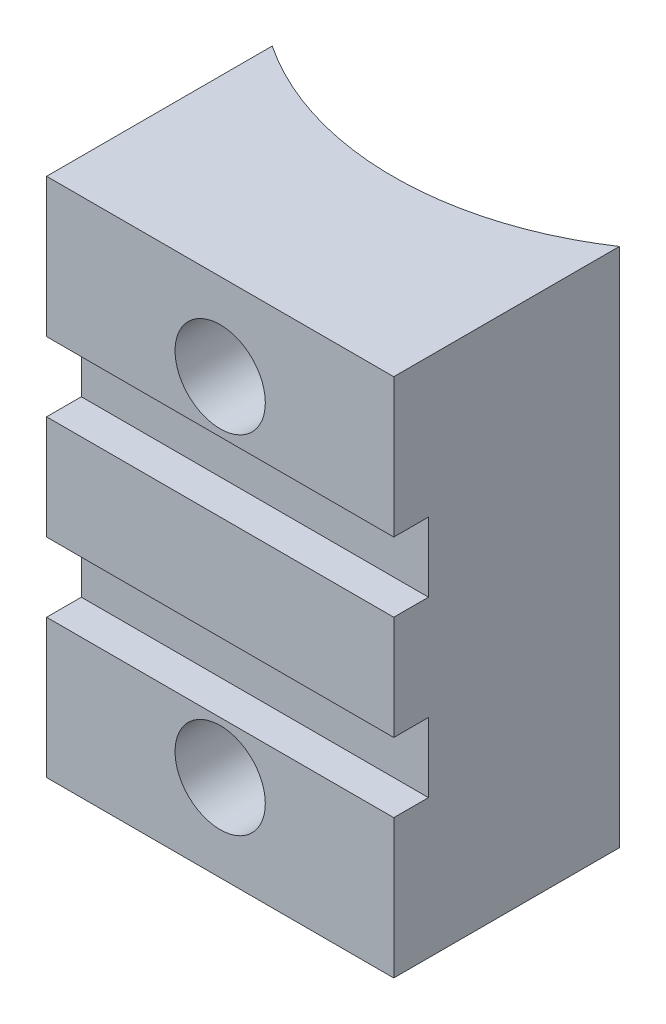
SolidWorks part; units mm, degrees
material "ABS"
ref_plane "Front Plane" through (0, 0, 0) normal (0, 0, 1) x (1, 0, 0)
ref_plane "Top Plane" through (0, 0, 0) normal (0, 1, 0) x (1, 0, 0)
ref_plane "Right Plane" through (0, 0, 0) normal (1, 0, 0) x (0, 0, -1)
sketch "Sketch1" plane through (0, 0, 0) normal (0, 1, 0) x (1, 0, 0)
  line L0 (0, 0) -> (20, 0)
  line L1 (20, 0) -> (20, 13)
  line L2 (0, 13) -> (0, 0)
  line L3 (10, 27.9666) -> (10, 0) construction
  arc A0 (20, 13) -> (0, 13) centre (10, 27.9666) cw
  dimension "D1" = 18
  dimension "D2" = 20
  dimension "D3" = 13
extrude "Boss-Extrude1" add sketch "Sketch1" along normal blind 30
sketch "Sketch2" plane through (0, 0, 0) normal (0, 0, 1) x (1, 0, 0)
  line L0 (10, 30) -> (10, 28.9885) construction
  line L1 (0, 30) -> (20, 30) construction
  line L2 (0, 0) -> (20, 0) construction
  circle A0 centre (10, 25) radius 2.6
  circle A2 centre (10, 5) radius 2.6
  dimension "D1" = 5.2
  dimension "D2" = 5
  dimension "D3" = 5
extrude "Cut-Extrude1" cut sketch "Sketch2" against normal up to next
sketch "Sketch3" plane through (0, 0, 0) normal (0, 0, 1) x (1, 0, 0)
  circle A0 centre (10, 25) radius 4.4
  circle A2 centre (10, 5) radius 4.4
  dimension "D1" = 8.8
extrude "Cut-Extrude2" cut sketch "Sketch3" against normal up to next from offset 4.5 offset against normal yes
sketch "Sketch4" plane through (20, 0, 0) normal (1, 0, 0) x (0, 0, -1)
  line L0 (0, 22) -> (2, 22)
  line L1 (0, 30) -> (0, 0) construction
  line L2 (2, 22) -> (2, 18)
  line L3 (2, 18) -> (0, 18)
  line L4 (0, 18) -> (0, 22)
  line L5 (0, 12) -> (2, 12)
  line L6 (2, 12) -> (2, 8)
  line L7 (2, 8) -> (0, 8)
  line L8 (0, 8) -> (0, 12)
  line L9 (0, 30) -> (13, 30) construction
  line L10 (0, 0) -> (13, 0) construction
  dimension "D1" = 4
  dimension "D2" = 2
  dimension "D3" = 8
  dimension "D4" = 8
extrude "Cut-Extrude3" cut sketch "Sketch4" against normal up to next
